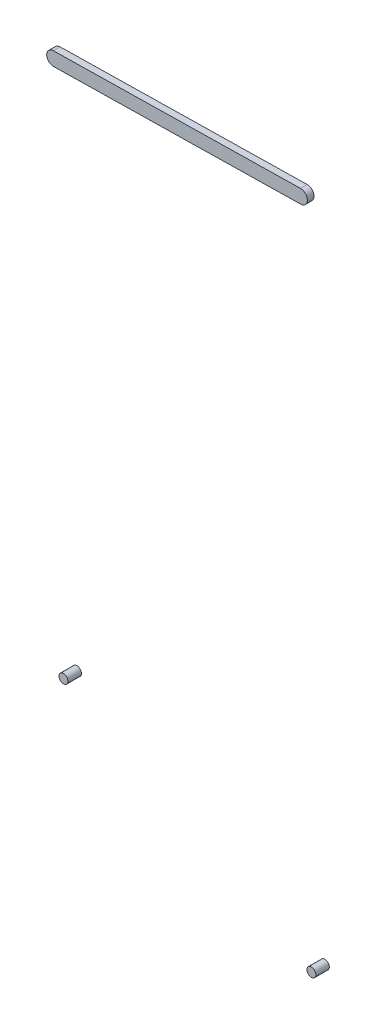
SolidWorks part; units mm, degrees
ref_plane "Front Plane" through (0, 0, 0) normal (0, 0, 1) x (1, 0, 0)
ref_plane "Top Plane" through (0, 0, 0) normal (0, 1, 0) x (1, 0, 0)
ref_plane "Right Plane" through (0, 0, 0) normal (1, 0, 0) x (0, 0, -1)
sketch "Sketch1" plane through (0, 0, 0) normal (0, 0, 1) x (1, 0, 0)
  line L0 (-55.0396, 14.0294) -> (0, 15) construction
  line L1 (-55.0662, 15.5404) -> (-0.0266, 16.511)
  line L2 (-55.0129, 12.5183) -> (0.0266, 13.489)
  arc A0 (-55.0662, 15.5404) -> (-55.0129, 12.5183) centre (-55.0396, 14.0294) ccw
  arc A1 (0.0266, 13.489) -> (-0.0266, 16.511) centre (0, 15) ccw
  point P4 (-27.5198, 14.5147)
extrude "Boss-Extrude1" add sketch "Sketch1" along normal blind 1.5 contours L2 A1 L1 A0
sketch "Sketch2" plane through (0, 0, 0) normal (0, 0, -1) x (-1, 0, 0)
  line L0 (-0.7257, -104.9978) -> (54.3139, -105.9684) construction
  line L1 (-0.6992, -103.498) -> (54.3403, -104.4687)
  line L2 (-0.7521, -106.4976) -> (54.2874, -107.4682)
  circle A0 centre (54.3139, -105.9684) radius 1 construction
  circle A1 centre (54.3139, -105.9684) radius 1
  arc A2 (-0.6992, -103.498) -> (-0.7521, -106.4976) centre (-0.7257, -104.9978) ccw
  arc A3 (54.2874, -107.4682) -> (54.3403, -104.4687) centre (54.3139, -105.9684) ccw
  circle A6 centre (-0.9071, -134.9973) radius 1 construction
  circle A7 centre (-0.9071, -134.9973) radius 1
  point P2 (26.7941, -105.4831)
  dimension "D1" = 3
extrude "Boss-Extrude2" add sketch "Sketch2" along normal blind 3 contours A7 | A1
